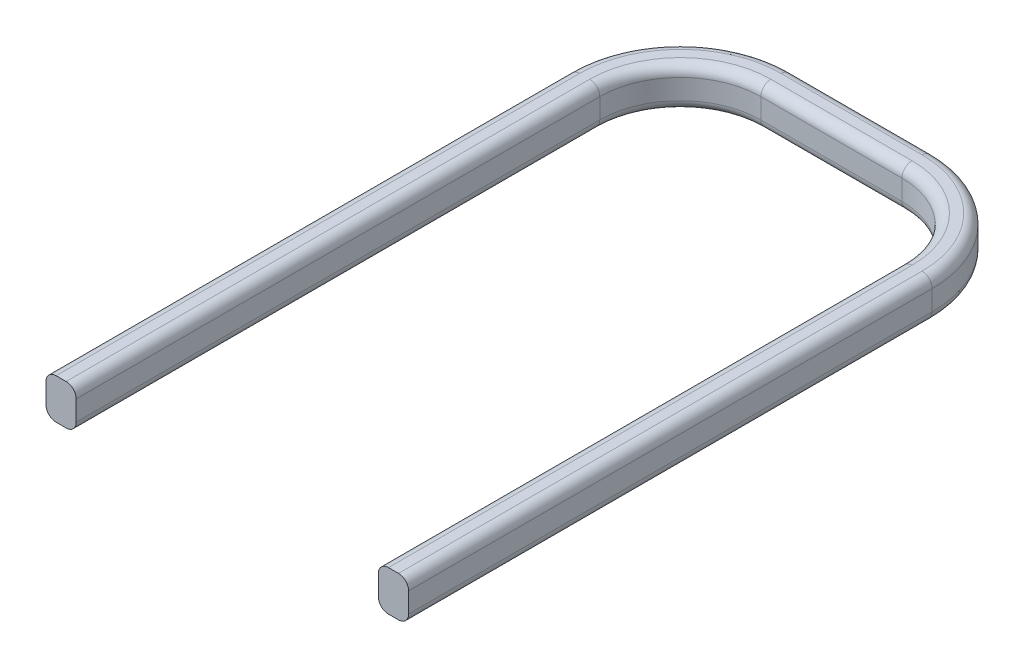
SolidWorks part; units mm, degrees
ref_plane "Front Plane" through (0, 0, 0) normal (0, 0, 1) x (1, 0, 0)
ref_plane "Top Plane" through (0, 0, 0) normal (0, 1, 0) x (1, 0, 0)
ref_plane "Right Plane" through (0, 0, 0) normal (1, 0, 0) x (0, 0, -1)
sketch "Sketch1" plane through (0, 0, 0) normal (0, 1, 0) x (1, 0, 0)
  line L0 (-3.95, 0) -> (-3.95, 13)
  line L1 (-1.95, 15) -> (1.5531, 15)
  line L2 (3.5531, 13) -> (3.5531, 0)
  arc A0 (-1.95, 15) -> (-3.95, 13) centre (-1.95, 13) ccw
  arc A1 (3.5531, 13) -> (1.5531, 15) centre (1.5531, 13) ccw
  point P8 (-3.95, 15)
  dimension "D3" = 2
  dimension "D4" = 2
  dimension "D1" = 3.95
  dimension "D2" = 15
sketch "Sketch2" plane through (0, 0, 0) normal (0, 0, 1) x (1, 0, 0)
  line L1 (-3.95, 0) -> (-4.7, 0)
  line L2 (-3.95, 0) -> (-3.95, 1)
  line L3 (-3.95, 1) -> (-4.7, 1)
  line L4 (-4.7, 0) -> (-4.7, 1)
  dimension "D1" = 0.75
  dimension "D2" = 1
sweep "Sweep1" add profiles "Sketch2" path "Sketch1"
fillet "Fillet1" radius 0.25 20 edges at (-3.95, 0, -6.5) (-3.3642, 0, -14.4142) (-0.1985, 0, -15) (2.9673, 0, -14.4142) (3.5531, 0, -6.5) (4.3031, 0, -6.5) (3.4976, 0, -14.9445) (-0.1985, 0, -15.75) (-3.8945, 0, -14.9445) (-4.7, 0, -6.5) (-4.7, 1, -6.5) (-3.8945, 1, -14.9445) (-0.1985, 1, -15.75) (3.4976, 1, -14.9445) (4.3031, 1, -6.5) (3.5531, 1, -6.5) (2.9673, 1, -14.4142) (-0.1985, 1, -15) (-3.3642, 1, -14.4142) (-3.95, 1, -6.5)
